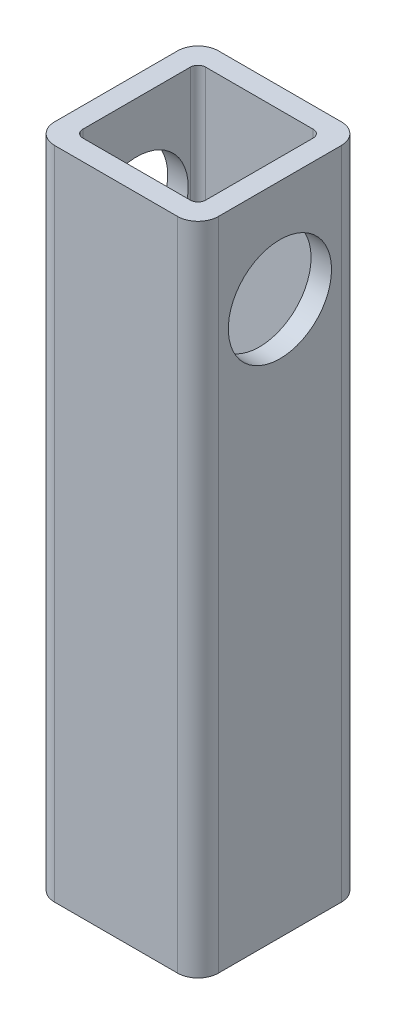
SolidWorks part; units mm, degrees
ref_plane "Front Plane" through (0, 0, 0) normal (0, 0, 1) x (1, 0, 0)
ref_plane "Top Plane" through (0, 0, 0) normal (0, 1, 0) x (1, 0, 0)
ref_plane "Right Plane" through (0, 0, 0) normal (1, 0, 0) x (0, 0, -1)
sketch "Sketch1" plane through (0, 0, 0) normal (0, 1, 0) x (0, 0, -1)
  line L1 (-19.05, 25.4) -> (19.05, 25.4)
  line L2 (-25.4, 19.05) -> (-25.4, -19.05)
  line L3 (-19.05, -25.4) -> (19.05, -25.4)
  line L4 (25.4, 19.05) -> (25.4, -19.05)
  line L5 (-25.4, 25.4) -> (25.4, -25.4) construction
  line L6 (-25.4, -25.4) -> (25.4, 25.4) construction
  line L7 (-16.6687, 19.05) -> (16.6687, 19.05)
  line L8 (-19.05, 16.6687) -> (-19.05, -16.6687)
  line L9 (-16.6687, -19.05) -> (16.6687, -19.05)
  line L10 (19.05, 16.6687) -> (19.05, -16.6687)
  line L11 (-19.05, 19.05) -> (19.05, -19.05) construction
  line L12 (-19.05, -19.05) -> (19.05, 19.05) construction
  arc A0 (-25.4, -19.05) -> (-19.05, -25.4) centre (-19.05, -19.05) ccw
  arc A1 (19.05, -25.4) -> (25.4, -19.05) centre (19.05, -19.05) ccw
  arc A2 (25.4, 19.05) -> (19.05, 25.4) centre (19.05, 19.05) ccw
  arc A3 (-19.05, 25.4) -> (-25.4, 19.05) centre (-19.05, 19.05) ccw
  arc A4 (-19.05, -16.6687) -> (-16.6687, -19.05) centre (-16.6687, -16.6687) ccw
  arc A5 (16.6687, -19.05) -> (19.05, -16.6687) centre (16.6687, -16.6687) ccw
  arc A6 (19.05, 16.6687) -> (16.6687, 19.05) centre (16.6687, 16.6687) ccw
  arc A7 (-16.6687, 19.05) -> (-19.05, 16.6687) centre (-16.6687, 16.6687) ccw
  point P0 (0, 0)
  point P6 (0, 0)
  dimension "D4" = 6.35
  dimension "D5" = 2.3813
  dimension "D1" = 50.8
  dimension "D2" = 50.8
  dimension "D3" = 6.35
extrude "Boss-Extrude1" add sketch "Sketch1" along normal mid plane 203.2
sketch "Sketch2" plane through (25.4, 0, 0) normal (1, 0, 0) x (0, 0, -1)
  line L0 (0, 69.85) -> (0, 0) construction
  line L1 (-19.05, 101.6) -> (19.05, 101.6) construction
  circle A0 centre (0, 69.85) radius 16.002
  dimension "D1" = 32.004
  dimension "D2" = 31.75
extrude "Cut-Extrude1" cut sketch "Sketch2" against normal through all
sketch "Sketch3" plane through (0, -101.6, 0) normal (0, -1, 0) x (1, 0, 0)
  line L0 (0, 25.4) -> (0, -25.4) construction
  line L1 (-19.05, 25.4) -> (19.05, 25.4) construction
  line L2 (19.05, -25.4) -> (-19.05, -25.4) construction
  line L3 (-25.4, 0) -> (25.4, 0) construction
  line L4 (-25.4, -19.05) -> (-25.4, 19.05) construction
  line L5 (25.4, 19.05) -> (25.4, -19.05) construction
